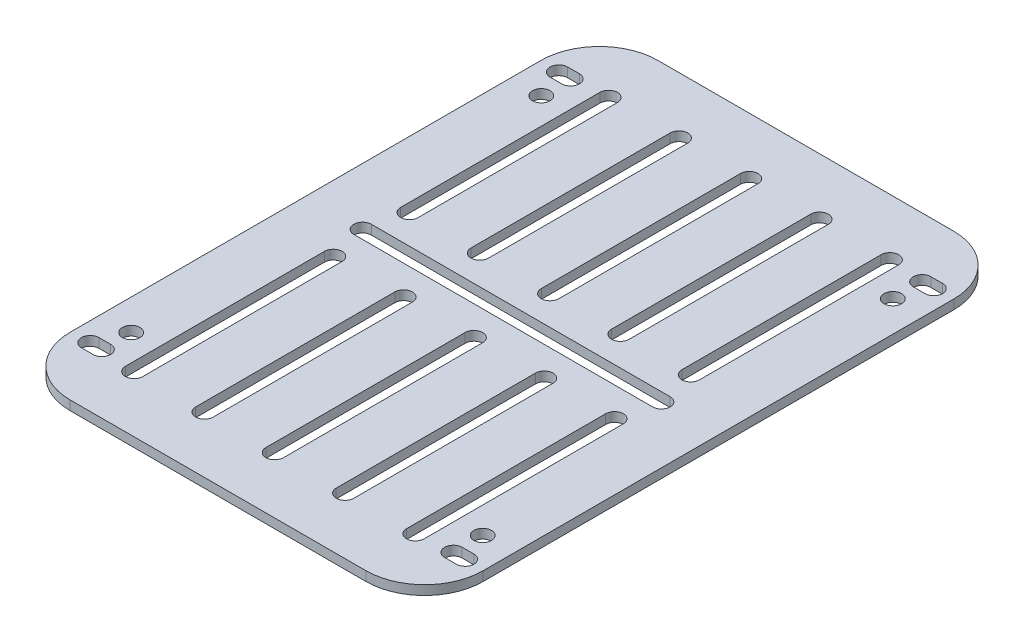
SolidWorks part; units mm, degrees
ref_plane "前基準面" through (0, 0, 0) normal (0, 0, 1) x (1, 0, 0)
ref_plane "上基準面" through (0, 0, 0) normal (0, 1, 0) x (1, 0, 0)
ref_plane "右基準面" through (0, 0, 0) normal (1, 0, 0) x (0, 0, -1)
sketch "草圖1" plane through (0, 0, 0) normal (0, 1, 0) x (1, 0, 0)
  line L0 (-54.1098, -98.8312) -> (-53.7471, -168.0916) construction
  line L1 (-55.1202, 51.9041) -> (-55.1202, -98.0959) construction
  line L2 (-25.5, 0) -> (25.5, 0) construction
  line L3 (-35.25, -50.175) -> (35.25, -50.175)
  line L4 (-35.25, -50.175) -> (-35.25, 50.175)
  line L5 (-35.25, 50.175) -> (35.25, 50.175)
  line L6 (35.25, -50.175) -> (35.25, 50.175)
  line L7 (0, 50.175) -> (0, -50.175) construction
  line L8 (-35.25, 0) -> (35.25, 0) construction
  line L9 (-25.5, 1.5) -> (25.5, 1.5)
  line L10 (-25.5, -1.5) -> (25.5, -1.5)
  line L11 (0, 40.5) -> (0, 6.5) construction
  line L12 (1.5, 40.5) -> (1.5, 6.5)
  line L13 (-1.5, 40.5) -> (-1.5, 6.5)
  line L14 (0, -40.5) -> (0, -6.5) construction
  line L15 (1.5, -40.5) -> (1.5, -6.5)
  line L16 (-1.5, -40.5) -> (-1.5, -6.5)
  line L17 (12, 40.5) -> (12, 6.5) construction
  line L18 (13.5, 40.5) -> (13.5, 6.5)
  line L19 (10.5, 40.5) -> (10.5, 6.5)
  line L20 (12, -40.5) -> (12, -6.5) construction
  line L21 (13.5, -40.5) -> (13.5, -6.5)
  line L22 (10.5, -40.5) -> (10.5, -6.5)
  line L23 (24, 40.5) -> (24, 6.5) construction
  line L24 (25.5, 40.5) -> (25.5, 6.5)
  line L25 (22.5, 40.5) -> (22.5, 6.5)
  line L26 (24, -40.5) -> (24, -6.5) construction
  line L27 (25.5, -40.5) -> (25.5, -6.5)
  line L28 (22.5, -40.5) -> (22.5, -6.5)
  line L29 (-24, -40.5) -> (-24, -6.5) construction
  line L30 (-25.5, -40.5) -> (-25.5, -6.5)
  line L31 (-22.5, -40.5) -> (-22.5, -6.5)
  line L32 (-12, -40.5) -> (-12, -6.5) construction
  line L33 (-13.5, -40.5) -> (-13.5, -6.5)
  line L34 (-10.5, -40.5) -> (-10.5, -6.5)
  line L35 (-12, 40.5) -> (-12, 6.5) construction
  line L36 (-13.5, 40.5) -> (-13.5, 6.5)
  line L37 (-10.5, 40.5) -> (-10.5, 6.5)
  line L38 (-24, 40.5) -> (-24, 6.5) construction
  line L39 (-25.5, 40.5) -> (-25.5, 6.5)
  line L40 (-22.5, 40.5) -> (-22.5, 6.5)
  line L41 (-32, 40) -> (-30, 40) construction
  line L42 (-32, 41.5) -> (-30, 41.5)
  line L43 (-32, 38.5) -> (-30, 38.5)
  line L44 (32, 40) -> (30, 40) construction
  line L45 (32, 41.5) -> (30, 41.5)
  line L46 (32, 38.5) -> (30, 38.5)
  line L47 (32, -40) -> (30, -40) construction
  line L48 (32, -41.5) -> (30, -41.5)
  line L49 (32, -38.5) -> (30, -38.5)
  line L50 (-32, -40) -> (-30, -40) construction
  line L51 (-32, -41.5) -> (-30, -41.5)
  line L52 (-32, -38.5) -> (-30, -38.5)
  arc A0 (-25.5, 1.5) -> (-25.5, -1.5) centre (-25.5, 0) ccw
  arc A1 (25.5, -1.5) -> (25.5, 1.5) centre (25.5, 0) ccw
  arc A2 (1.5, 40.5) -> (-1.5, 40.5) centre (0, 40.5) ccw
  arc A3 (-1.5, 6.5) -> (1.5, 6.5) centre (0, 6.5) ccw
  arc A4 (1.5, -40.5) -> (-1.5, -40.5) centre (0, -40.5) cw
  arc A5 (-1.5, -6.5) -> (1.5, -6.5) centre (0, -6.5) cw
  arc A6 (13.5, 40.5) -> (10.5, 40.5) centre (12, 40.5) ccw
  arc A7 (10.5, 6.5) -> (13.5, 6.5) centre (12, 6.5) ccw
  arc A8 (13.5, -40.5) -> (10.5, -40.5) centre (12, -40.5) cw
  arc A9 (10.5, -6.5) -> (13.5, -6.5) centre (12, -6.5) cw
  arc A10 (25.5, 40.5) -> (22.5, 40.5) centre (24, 40.5) ccw
  arc A11 (22.5, 6.5) -> (25.5, 6.5) centre (24, 6.5) ccw
  arc A12 (25.5, -40.5) -> (22.5, -40.5) centre (24, -40.5) cw
  arc A13 (22.5, -6.5) -> (25.5, -6.5) centre (24, -6.5) cw
  arc A14 (-25.5, -40.5) -> (-22.5, -40.5) centre (-24, -40.5) ccw
  arc A15 (-22.5, -6.5) -> (-25.5, -6.5) centre (-24, -6.5) ccw
  arc A16 (-13.5, -40.5) -> (-10.5, -40.5) centre (-12, -40.5) ccw
  arc A17 (-10.5, -6.5) -> (-13.5, -6.5) centre (-12, -6.5) ccw
  arc A18 (-13.5, 40.5) -> (-10.5, 40.5) centre (-12, 40.5) cw
  arc A19 (-10.5, 6.5) -> (-13.5, 6.5) centre (-12, 6.5) cw
  arc A20 (-25.5, 40.5) -> (-22.5, 40.5) centre (-24, 40.5) cw
  arc A21 (-22.5, 6.5) -> (-25.5, 6.5) centre (-24, 6.5) cw
  circle A22 centre (-30, 35) radius 1.5
  circle A23 centre (30, 35) radius 1.5
  circle A24 centre (-30, -35) radius 1.5
  circle A25 centre (30, -35) radius 1.5
  arc A26 (-32, 41.5) -> (-32, 38.5) centre (-32, 40) ccw
  arc A27 (-30, 38.5) -> (-30, 41.5) centre (-30, 40) ccw
  arc A28 (32, 41.5) -> (32, 38.5) centre (32, 40) cw
  arc A29 (30, 38.5) -> (30, 41.5) centre (30, 40) cw
  arc A30 (32, -41.5) -> (32, -38.5) centre (32, -40) ccw
  arc A31 (30, -38.5) -> (30, -41.5) centre (30, -40) ccw
  arc A32 (-32, -41.5) -> (-32, -38.5) centre (-32, -40) cw
  arc A33 (-30, -38.5) -> (-30, -41.5) centre (-30, -40) cw
  point P4 (0, 0)
  point P9 (0, 0)
  point P19 (0, 23.5)
  point P26 (12, 23.5)
  point P29 (0, -23.5)
  point P42 (12, -23.5)
  point P48 (24, 23.5)
  point P56 (24, -23.5)
  point P63 (-24, -23.5)
  point P70 (-12, -23.5)
  point P77 (-12, 23.5)
  point P84 (-24, 23.5)
  point P91 (0, -23.5)
  point P98 (-31, 40)
  point P114 (31, 40)
  point P121 (31, -40)
  point P128 (-31, -40)
  dimension "D11" = 3
  dimension "D1" = 150
  dimension "D2" = 70.5
  dimension "D3" = 100.35
  dimension "D4" = 3
  dimension "D5" = 51
  dimension "D6" = 3
  dimension "D7" = 34
  dimension "D8" = 23.5
  dimension "D10" = 12
  dimension "D12" = 3
  dimension "D13" = 2
  dimension "D14" = 60
  dimension "D15" = 70
  dimension "D16" = 62
  dimension "D17" = 80
  dimension "D9" = 3
extrude "填料-伸長1" add sketch "草圖1" along normal blind 1.6
fillet "圓角1" radius 10 4 edges at (-35.25, 0.8, -50.175) (35.25, 0.8, -50.175) (-35.25, 0.8, 50.175) (35.25, 0.8, 50.175)
